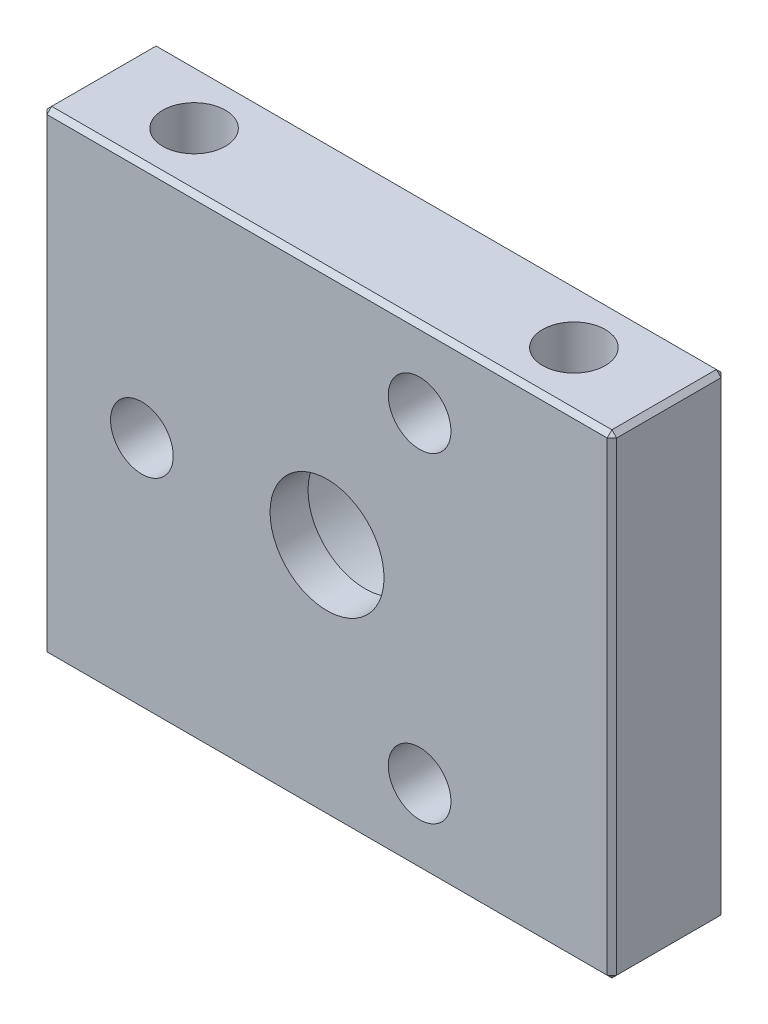
SolidWorks part; units mm, degrees
material "1060 Alloy"
ref_plane "Front Plane" through (0, 0, 0) normal (0, 0, 1) x (1, 0, 0)
ref_plane "Top Plane" through (0, 0, 0) normal (0, 1, 0) x (1, 0, 0)
ref_plane "Right Plane" through (0, 0, 0) normal (1, 0, 0) x (0, 0, -1)
sketch "Sketch1" plane through (0, 0, 0) normal (0, 1, 0) x (1, 0, 0)
  line L0 (-15, -3) -> (15, 3) construction
  line L1 (-15, 3) -> (15, 3)
  line L2 (-15, 3) -> (-15, -3)
  line L3 (-15, -3) -> (15, -3)
  line L4 (15, 3) -> (15, -3)
  point P4 (0, 0)
  dimension "D1" = 6
  dimension "D2" = 30
extrude "Extrude1" add sketch "Sketch1" along normal blind 25
sketch "Sketch2" plane through (0, 0, -3) normal (0, 0, -1) x (-1, 0, 0)
  line L0 (-15, 0) -> (15, 25) construction
  circle A0 centre (0, 12.5) radius 5
  dimension "D1" = 10
extrude "Cut-Extrude1" cut sketch "Sketch2" against normal blind 4
sketch "Sketch3" plane through (0, 0, 1) normal (0, 0, -1) x (-1, 0, 0)
  circle A0 centre (0, 12.5) radius 3
  circle A1 centre (0, 12.5) radius 5 construction
  dimension "D1" = 6
extrude "Cut-Extrude2" cut sketch "Sketch3" against normal blind 12
hole_wizard "M4x0.7 Tapped Hole1" positions "3DSketch1" profile "Sketch5" tap size "M4x0.7" standard "Ansi Metric"
sketch3d "3DSketch1"
  line L0 (-12.7688, 25, -3) -> (-12.7688, 25, 3) construction
  line L1 (15, 25, -3) -> (-15, 25, -3) construction
  line L2 (-15, 25, 3) -> (15, 25, 3) construction
  line L3 (-15, 25, -3) -> (-15, 25, 3) construction
  line L4 (15, 25, 3) -> (15, 25, -3) construction
  point P0 (10, 25, 0)
  point P2 (-10, 25, 0)
  point P5 (10, 0, 0)
  point P7 (-10, 0, 0)
  point P17 (-12.7688, 25, 0)
  dimension "D1" = 5
  dimension "D2" = 5
sketch "Sketch5" plane through (10, 25, 0) normal (1, 0, 0) x (0, 0, 1)
  line L0 (0, 0) -> (0, 11.2914)
  line L1 (0, 11.2914) -> (1.65, 10.3)
  line L2 (1.65, 10.3) -> (1.65, 0)
  line L5 (1.65, 0) -> (0, 0)
  line L10 (0, 11.2914) -> (-1.65, 10.3) construction
  line L11 (0, -6.35) -> (0, 107.95) construction
  dimension "Tap Drill Dia." = 3.3
  dimension "Tap Drill Depth" = 10.3
  dimension "Drill Angle" = 118
cosmetic thread "Hole Thread1" parameters "D1"=8.2, "D2"=4
cosmetic thread "Hole Thread2" parameters "D1"=8.2, "D2"=4
cosmetic thread "Hole Thread3" parameters "D1"=8.2, "D2"=4
cosmetic thread "Hole Thread4" parameters "D1"=8.2, "D2"=4
chamfer "Chamfer2" distance 0.25 angle 45 12 edges at (15, 12.5, 3) (15, 25, 0) (15, 12.5, -3) (15, 0, 0) (-15, 12.5, -3) (0, 25, -3) (-15, 25, 0) (0, 0, -3) (-15, 0, 0) (0, 0, 3) (-15, 12.5, 3) (0, 25, 3)
hole_wizard "M4x0.7 Tapped Hole2" positions "3DSketch2" profile "Sketch6" tap size "M4x0.7" standard "Ansi Metric"
sketch3d "3DSketch2"
  line L1 (0, 12.5, 3) -> (-9.75, 12.5, 3) construction
  line L2 (0, 12.5, 3) -> (0, 12.5, 1) construction
  line L4 (4.875, 4.0563, 3) -> (0, 12.5, 3) construction
  line L6 (0, 12.5, 3) -> (4.875, 20.9437, 3) construction
  point P0 (-9.75, 12.5, 3)
  point P2 (4.875, 4.0563, 3)
  point P4 (4.875, 20.9437, 3)
  dimension "D1" = 9.75
  dimension "D2" = 120
  dimension "D3" = 9.75
  dimension "D4" = 9.75
  dimension "D5" = 120
sketch "Sketch6" plane through (-9.75, 12.5, 3) normal (1, 0, 0) x (0, -1, 0)
  line L0 (0, 0) -> (0, 11.0914)
  line L1 (0, 11.0914) -> (1.65, 10.1)
  line L2 (1.65, 10.1) -> (1.65, 0)
  line L5 (1.65, 0) -> (0, 0)
  line L10 (0, 11.0914) -> (-1.65, 10.1) construction
  line L11 (0, -6.35) -> (0, 107.95) construction
  dimension "Tap Drill Dia." = 3.3
  dimension "Tap Drill Depth" = 10.1
  dimension "Drill Angle" = 118
cosmetic thread "Hole Thread5" parameters "D1"=6, "D2"=4
cosmetic thread "Hole Thread6" parameters "D1"=6, "D2"=4
cosmetic thread "Hole Thread7" parameters "D1"=6, "D2"=4
